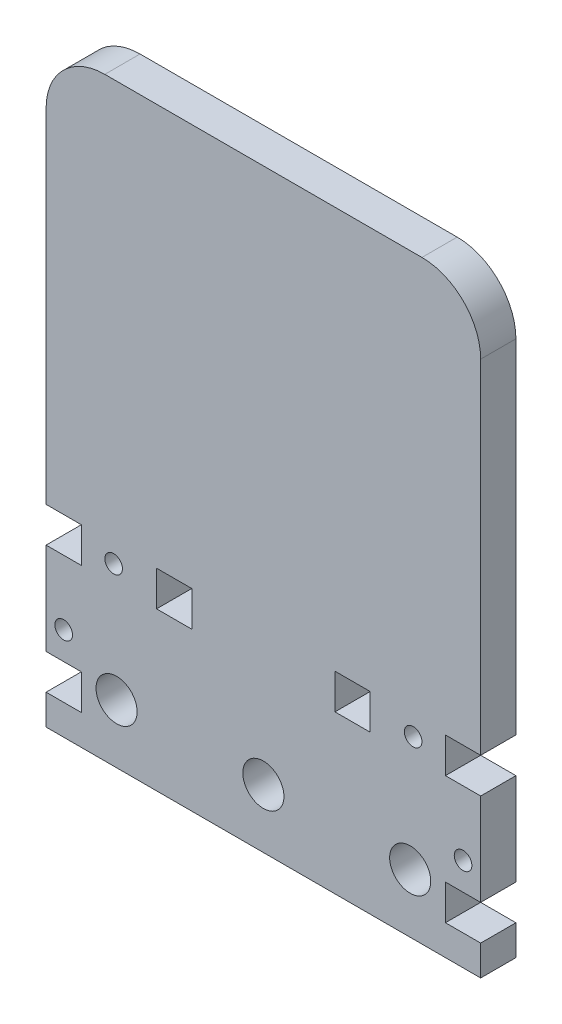
SolidWorks part; units mm, degrees
ref_plane "Front Plane" through (0, 0, 0) normal (0, 0, 1) x (1, 0, 0)
ref_plane "Top Plane" through (0, 0, 0) normal (0, 1, 0) x (1, 0, 0)
ref_plane "Right Plane" through (0, 0, 0) normal (1, 0, 0) x (0, 0, -1)
sketch "Sketch1" plane through (0, 0, 0) normal (0, 0, 1) x (1, 0, 0)
  line L0 (37, 101.26) -> (37, 0) construction
  line L1 (0, 0) -> (74, 0)
  line L2 (0, 0) -> (0, 91.26)
  line L3 (10, 101.26) -> (64, 101.26)
  line L4 (74, 0) -> (74, 91.26)
  line L5 (74, 5.15) -> (68, 5.15)
  line L6 (0, 32.84) -> (6, 32.84)
  line L7 (0, 32.84) -> (0, 26.84)
  line L8 (0, 26.84) -> (6, 26.84)
  line L9 (6, 32.84) -> (6, 26.84)
  line L10 (0, 11.15) -> (6, 11.15)
  line L11 (0, 11.15) -> (0, 5.15)
  line L12 (0, 5.15) -> (6, 5.15)
  line L13 (6, 11.15) -> (6, 5.15)
  line L14 (68, 11.15) -> (68, 5.15)
  line L15 (74, 11.15) -> (68, 11.15)
  line L16 (74, 26.84) -> (68, 26.84)
  line L17 (68, 32.84) -> (68, 26.84)
  line L18 (74, 32.84) -> (68, 32.84)
  line L19 (49.19, 32.84) -> (49.19, 26.84)
  line L20 (18.81, 32.84) -> (24.81, 32.84)
  line L21 (18.81, 32.84) -> (18.81, 26.84)
  line L22 (18.81, 26.84) -> (24.81, 26.84)
  line L23 (24.81, 32.84) -> (24.81, 26.84)
  line L24 (55.19, 26.84) -> (49.19, 26.84)
  line L25 (55.19, 32.84) -> (55.19, 26.84)
  line L26 (55.19, 32.84) -> (49.19, 32.84)
  arc A0 (64, 101.26) -> (74, 91.26) centre (64, 91.26) cw
  arc A1 (0, 91.26) -> (10, 101.26) centre (10, 91.26) cw
  circle A2 centre (37, 10) radius 3.5
  circle A3 centre (12, 10) radius 3.5
  circle A4 centre (62, 10) radius 3.5
  point P9 (0, 101.26)
  dimension "D3" = 10
  dimension "D4" = 7
  dimension "D5" = 7
  dimension "D6" = 50
  dimension "D1" = 74
  dimension "D2" = 101.26
  dimension "D7" = 10
  dimension "D8" = 10
  dimension "D9" = 6
  dimension "D10" = 6
  dimension "D11" = 6
  dimension "D12" = 6
  dimension "D13" = 6
  dimension "D14" = 5.15
  dimension "D15" = 26.84
  dimension "D16" = 6
  dimension "D17" = 12.81
extrude "Boss-Extrude1" add sketch "Sketch1" along normal blind 6 contours L0 L3 A1 L2 L6 L9 L8 L10 L13 L12 L1 A2 L20 L23 L22 L21 A3 | L3 L0 A2 L1 L4 L5 L14 L15 L16 L17 L18 A0 A4 L26 L25 L24 L19
sketch "Sketch2" plane through (0, 0, 6) normal (0, 0, 1) x (1, 0, 0)
  line L0 (0, 11.15) -> (6, 11.15) construction
  line L1 (6, 32.84) -> (6, 26.84) construction
  line L2 (0, 26.84) -> (6, 26.84) construction
  line L3 (0, 32.84) -> (0, 91.26) construction
  line L4 (37, 101.26) -> (37, 0) construction
  line L5 (10, 101.26) -> (64, 101.26) construction
  line L6 (0, 0) -> (74, 0) construction
  circle A0 centre (3, 15.84) radius 1.5
  circle A1 centre (11.5, 29.84) radius 1.5
  circle A2 centre (62.5, 29.84) radius 1.5
  circle A3 centre (71, 15.84) radius 1.5
  point P4 (3, 11.15)
  point P9 (6, 29.84)
  dimension "D1" = 3
  dimension "D2" = 3
  dimension "D3" = 11
  dimension "D4" = 11.5
extrude "Cut-Extrude1" cut sketch "Sketch2" against normal up to next
